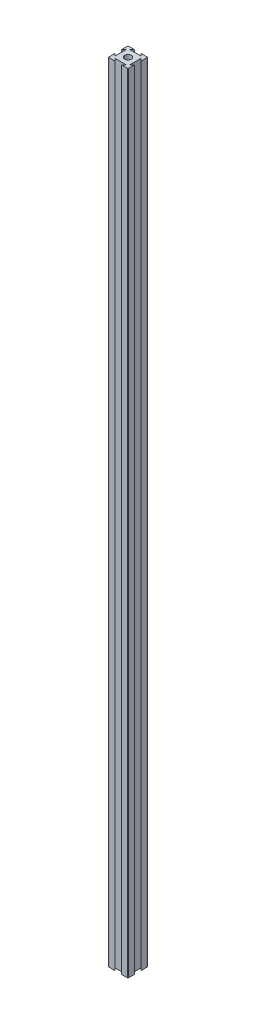
SolidWorks part; units mm, degrees
material "Alumina"
ref_plane "Front Plane" through (0, 0, 0) normal (0, 0, 1) x (1, 0, 0)
ref_plane "Top Plane" through (0, 0, 0) normal (0, 1, 0) x (1, 0, 0)
ref_plane "Right Plane" through (0, 0, 0) normal (1, 0, 0) x (0, 0, -1)
sketch "Sketch1" plane through (0, 0, 0) normal (0, 1, 0) x (1, 0, 0)
  line L0 (6.6667, 20) -> (4.285, 17.6183)
  line L1 (0, 0) -> (20, 0)
  line L2 (0, 0) -> (0, 20)
  line L3 (0, 20) -> (20, 20)
  line L4 (20, 0) -> (20, 20)
  line L5 (4.285, 17.6183) -> (15.715, 17.6183)
  line L6 (15.715, 17.6183) -> (13.3333, 20)
  line L7 (13.3333, 20) -> (6.6667, 20)
  line L8 (0, 10) -> (20, 10) construction
  line L9 (10, 20) -> (10, 0) construction
  line L10 (15.715, 2.3817) -> (13.3333, 0)
  line L11 (4.285, 2.3817) -> (15.715, 2.3817)
  line L12 (6.6667, 0) -> (4.285, 2.3817)
  line L13 (13.3333, 0) -> (6.6667, 0)
  line L14 (0, 13.3333) -> (2.3817, 15.715)
  line L15 (2.3817, 15.715) -> (2.3817, 4.285)
  line L16 (2.3817, 4.285) -> (0, 6.6667)
  line L17 (0, 6.6667) -> (0, 13.3333)
  line L18 (17.6183, 4.285) -> (20, 6.6667)
  line L19 (17.6183, 15.715) -> (17.6183, 4.285)
  line L20 (20, 13.3333) -> (17.6183, 15.715)
  line L21 (20, 6.6667) -> (20, 13.3333)
  circle A0 centre (10, 10) radius 3.3333
  dimension "D1" = 20
  dimension "D2" = 20
  dimension "D3" = 6.6667
  dimension "D4" = 6.6667
  dimension "D5" = 45
  dimension "D6" = 45
  dimension "D7" = 11.43
  dimension "D8" = 6.6667
  dimension "D9" = 6.6667
  dimension "D10" = 11.43
  dimension "D11" = 45
  dimension "D12" = 45
extrude "Boss-Extrude1" add sketch "Sketch1" along normal blind 800.1 contours L20 L4 L3 L6 L5 L0 L2 L14 L15 L16 L1 L12 L11 L10 L18 L19 A0
fillet "Fillet4" radius 0.508 4 edges at (0, 400.05, -20) (20, 400.05, -20) (0, 400.05, 0) (20, 400.05, 0)
